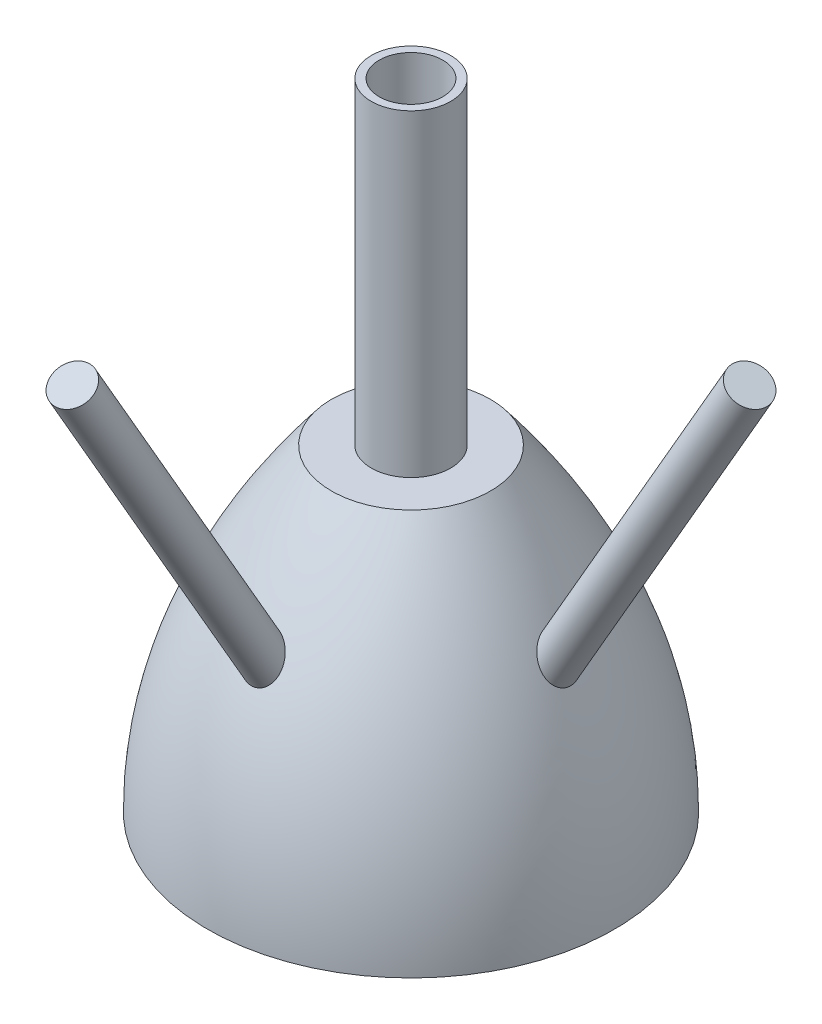
SolidWorks part; units mm, degrees
other "Markup1"
sketch "Sketch7" plane through (1376.2, 3000, 1376.2) normal (0.141, 0.2725, 0.9518) x (0.9395, 0.2663, -0.2155)
material "AISI 321 Annealed Stainless Steel (SS)"
ref_plane "Front Plane" through (0, 0, 0) normal (0, 0, 1) x (1, 0, 0)
ref_plane "Top Plane" through (0, 0, 0) normal (0, 1, 0) x (1, 0, 0)
ref_plane "Right Plane" through (0, 0, 0) normal (1, 0, 0) x (0, 0, -1)
sketch "Sketch1" plane through (0, 0, 0) normal (0, 0, 1) x (1, 0, 0)
  line L0 (0, 0) -> (650, 0) construction
  line L7 (0, 0) -> (650, 0)
  line L8 (254, 1014.6921) -> (0, 1014.6921)
  line L9 (0, 1014.6921) -> (0, 0)
  parabola Q0 (650, 0) -> (254, 1014.6921) focus (0, 0) apex (650, 0)
  dimension "D1" = 650
  dimension "D2" = 254
revolve "Revolve1" add sketch "Sketch1" angle 360 about L9
shell "Shell1" thickness 50.8
sketch "Sketch2" plane through (0, 1014.6921, 0) normal (0, 1, 0) x (1, 0, 0)
  circle A1 centre (0, 0) radius 127
  circle A3 centre (0, 0) radius 254 construction
  dimension "D1" = 127
extrude "Boss-Extrude1" add sketch "Sketch2" along normal blind 1014.6921
sketch "Sketch8" plane through (0, 2029.3841, 0) normal (0, 1, 0) x (1, 0, 0)
  circle A0 centre (0, 0) radius 50.8
  circle A1 centre (0, 0) radius 127 construction
  dimension "D1" = 76.2
extrude "Cut-Extrude1" cut sketch "Sketch8" against normal offset from surface (989.2921 mm away) 76.2 contours A0 up to face at (-229.0587, 963.8921, 0)
sketch "Sketch9" plane through (0, 963.8921, 0) normal (0, -1, 0) x (1, 0, 0)
  circle A0 centre (0, 0) radius 101.6
  dimension "D1" = 203.2
extrude "Cut-Extrude2" cut sketch "Sketch9" against normal up to next
fillet "Fillet2" radius 127 1 edges at (-229.0587, 963.8921, 0)
sketch "Sketch4" plane through (0, 0, 0) normal (1, 0, 0) x (0, 0, -1)
  line L0 (0, 0) -> (1166.7896, 673.6463) construction
  line L1 (1513.82, 0) -> (-1513.82, 0) construction
  dimension "D1" = 30
ref_plane "Plane4" through (0, 0, 0) normal (0, 0.866, 0.5) x (0, 0.5, -0.866)
ref_plane "Plane5" through (0.0002, 1759.7636, 1016) normal (0, 0.866, 0.5) x (0, 0.5, -0.866)
sketch "Sketch5" plane through (0.0002, 1759.7636, 1016) normal (0, 0.866, 0.5) x (0, 0.5, -0.866)
  line L0 (0, 0) -> (1347.2926, 0) construction
  line L1 (-76.2, 0) -> (0, 0) construction
  circle A0 centre (-76.2, 0) radius 63.5
  dimension "D1" = 127
  dimension "D2" = 76.2
extrude "Boss-Extrude4" add sketch "Sketch5" against normal up to surface (1254.2875 mm away)
pattern_circular "CirPattern1" count 2 every 90 about axis through (0, 2029.3841, 0) along (0, -1, 0) of "Boss-Extrude4"
